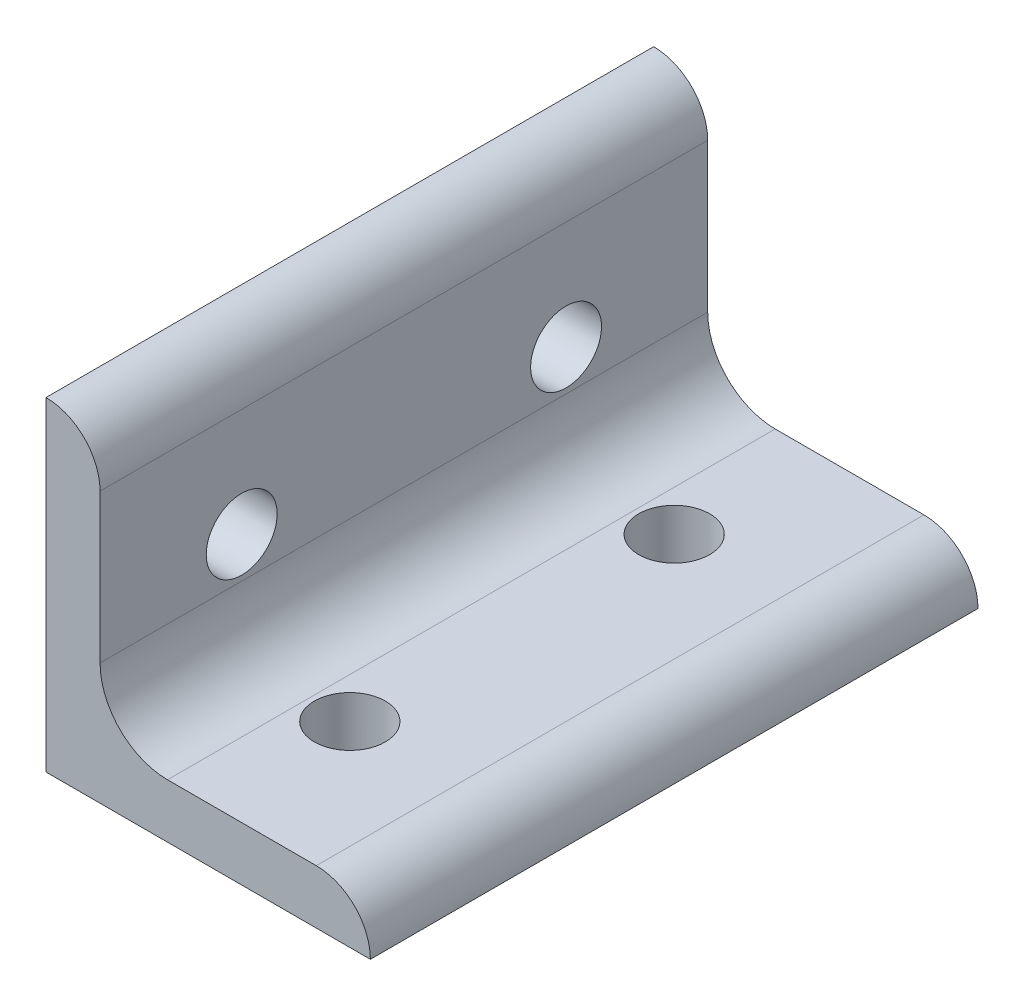
SolidWorks part; units mm, degrees
ref_plane "Front Plane" through (0, 0, 0) normal (0, 0, 1) x (1, 0, 0)
ref_plane "Top Plane" through (0, 0, 0) normal (0, 1, 0) x (1, 0, 0)
ref_plane "Right Plane" through (0, 0, 0) normal (1, 0, 0) x (0, 0, -1)
sketch "Sketch1" plane through (0, 0, 0) normal (0, 0, 1) x (1, 0, 0)
  line L0 (0, 0) -> (0, 38.1) construction
  line L1 (6.35, 31.75) -> (6.35, 38.1) construction
  line L2 (6.35, 31.75) -> (6.35, 14.2748) construction
  line L3 (14.2748, 6.35) -> (31.75, 6.35) construction
  line L4 (6.35, 38.1) -> (0, 38.1) construction
  line L5 (38.1, 0) -> (0, 0) construction
  line L6 (31.75, 6.35) -> (38.1, 6.35) construction
  line L7 (38.1, 6.35) -> (38.1, 0) construction
  arc A0 (6.35, 31.75) -> (0, 38.1) centre (0, 31.75) ccw construction
  arc A1 (38.1, 0) -> (31.75, 6.35) centre (31.75, 0) ccw construction
  arc A2 (6.35, 14.2748) -> (14.2748, 6.35) centre (14.2748, 14.2748) ccw construction
  point P10 (6.35, 34.925)
  dimension "D1" = 7.9248
  dimension "Height C" = 38.1
  dimension "Width B" = 38.1
  dimension "Thickness C" = 6.35
sketch "Sketch2" plane through (0, 0, 0) normal (1, 0, 0) x (0, 0, -1)
  line L0 (35.687, 0) -> (-35.687, 0)
  point P4 (0, 0)
  dimension "Length" = 71.374
sketch "Sketch4" plane through (0, 0, 0) normal (0, 0, 1) x (1, 0, 0)
  line L0 (38.1, 0) -> (0, 0) construction
  line L1 (14.2748, 6.35) -> (31.75, 6.35) construction
  line L2 (6.35, 31.75) -> (6.35, 14.2748) construction
  line L3 (0, 0) -> (0, 38.1) construction
  line L4 (38.1, 0) -> (0, 0)
  line L5 (14.2748, 6.35) -> (31.75, 6.35)
  line L6 (6.35, 31.75) -> (6.35, 14.2748)
  line L7 (0, 0) -> (0, 38.1)
  arc A0 (38.1, 0) -> (31.75, 6.35) centre (31.75, 0) ccw construction
  arc A1 (6.35, 14.2748) -> (14.2748, 6.35) centre (14.2748, 14.2748) ccw construction
  arc A2 (6.35, 31.75) -> (0, 38.1) centre (0, 31.75) ccw construction
  arc A3 (38.1, 0) -> (31.75, 6.35) centre (31.75, 0) ccw
  arc A4 (6.35, 14.2748) -> (14.2748, 6.35) centre (14.2748, 14.2748) ccw
  arc A5 (6.35, 31.75) -> (0, 38.1) centre (0, 31.75) ccw
extrude "Boss-Extrude1" add sketch "Sketch4" along normal up to vertex (35.687 mm away) and the other way up to vertex (35.687 mm away) up to point (0, 0, 35.687) other way up to point (0, 0, -35.687)
sketch "Sketch3" plane through (0, 0, 0) normal (0, 1, 0) x (1, 0, 0)
  line L0 (38.1, -35.687) -> (38.1, 35.687) construction
  circle A0 centre (19.05, -19.05) radius 4.1656
  circle A1 centre (19.05, 19.05) radius 4.1656
  dimension "D1" = 19.05
  dimension "D2" = 19.05
extrude "Cut-Extrude1" cut sketch "Sketch3" along normal through all
sketch "Sketch5" plane through (0, 0, 0) normal (1, 0, 0) x (0, 0, -1)
  line L0 (-35.687, 38.1) -> (35.687, 38.1) construction
  line L3 (19.05, 19.05) -> (-19.05, 19.05) construction
  circle A0 centre (-19.05, 19.05) radius 4.1656
  circle A1 centre (19.05, 19.05) radius 4.1656
  dimension "D2" = 8.3312
  dimension "D1" = 19.05
  dimension "D3" = 38.1
  dimension "D4" = 19.05
extrude "Cut-Extrude2" cut sketch "Sketch5" along normal through all
equation "\"D1@Sketch5\"=\"D1@Sketch3\""
equation "\"D2@Sketch5\"=\"E@Sketch3\""
equation "\"D3@Sketch5\"=\"D3@Sketch3\""
equation "\"D4@Sketch5\"=\"D2@Sketch3\""
